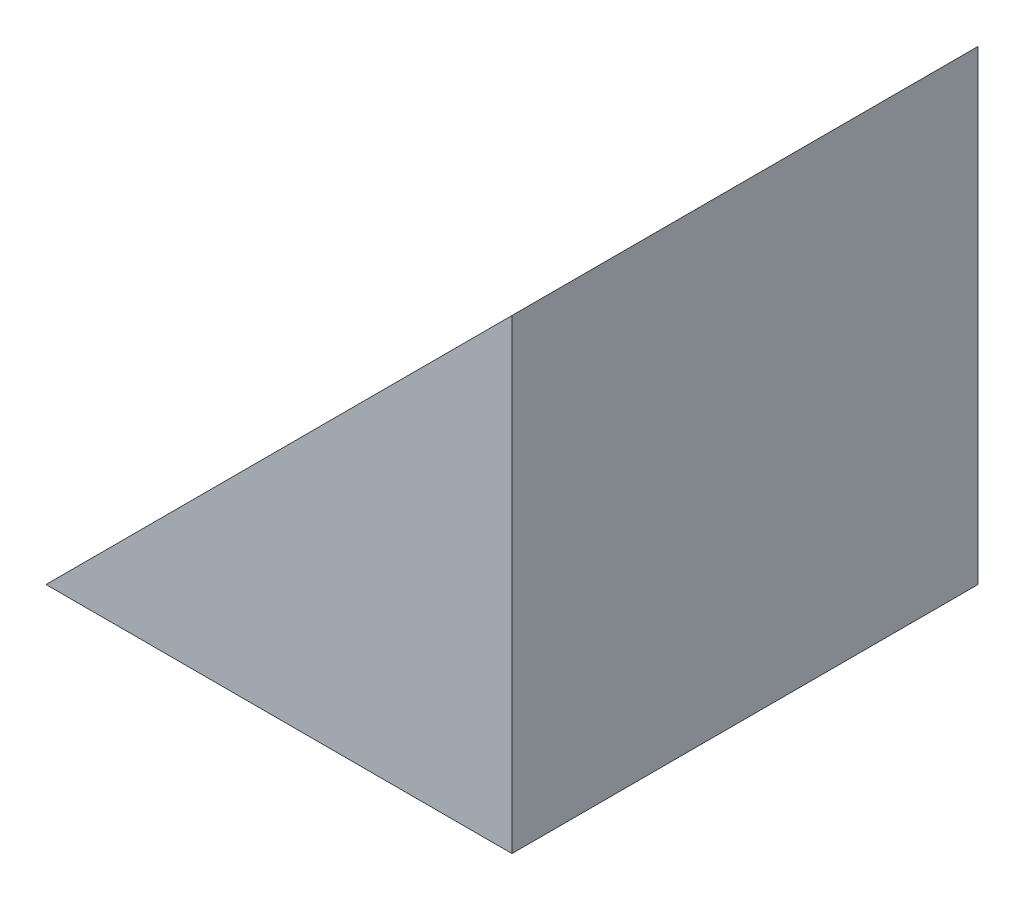
SolidWorks part; units mm, degrees
ref_plane "前视基准面" through (0, 0, 0) normal (0, 0, 1) x (1, 0, 0)
ref_plane "上视基准面" through (0, 0, 0) normal (0, 1, 0) x (1, 0, 0)
ref_plane "右视基准面" through (0, 0, 0) normal (1, 0, 0) x (0, 0, -1)
sketch "草图1" plane through (0, 0, 0) normal (0, 0, 1) x (1, 0, 0)
  line L0 (69.8856, 53.1116) -> (69.8856, 73.1116)
  line L1 (69.8856, 53.1116) -> (49.8856, 53.1116)
  line L2 (49.8856, 53.1116) -> (69.8856, 73.1116)
  dimension "D1" = 20
  dimension "D2" = 20
extrude "凸台-拉伸1" add sketch "草图1" along normal blind 20 contours L2 L0 L1
